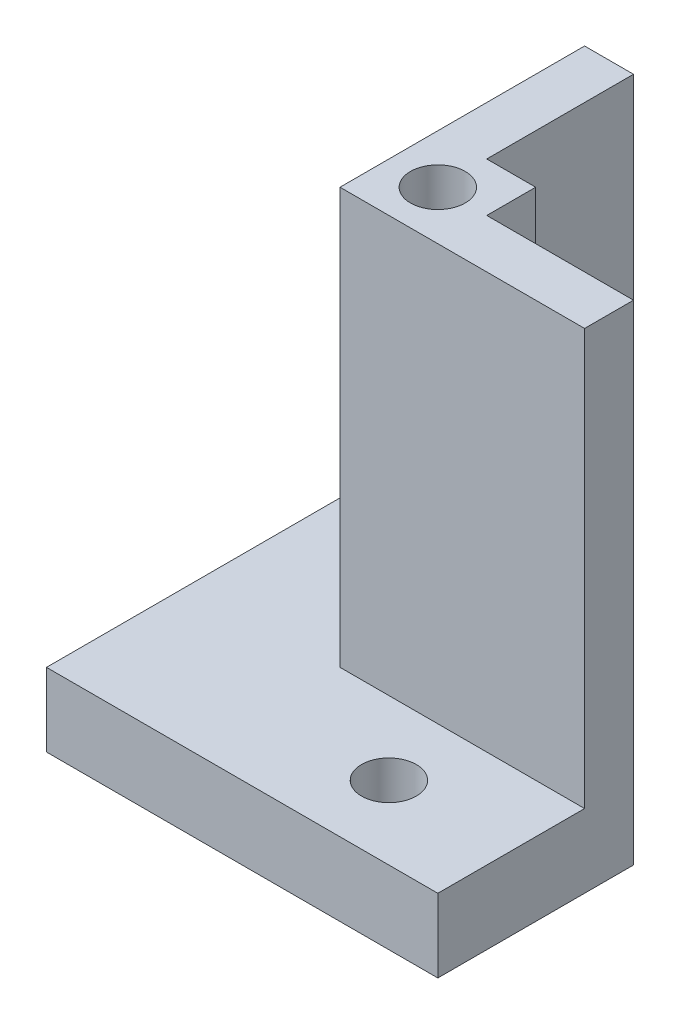
SolidWorks part; units mm, degrees
material "6061-T6 (SS)"
ref_plane "Front Plane" through (0, 0, 0) normal (0, 0, 1) x (1, 0, 0)
ref_plane "Top Plane" through (0, 0, 0) normal (0, 1, 0) x (1, 0, 0)
ref_plane "Right Plane" through (0, 0, 0) normal (1, 0, 0) x (0, 0, -1)
sketch "Sketch4" plane through (0, 0, 0) normal (0, 1, 0) x (1, 0, 0)
  line L0 (-2.7325, 2.4892) -> (-2.7325, 10.1092)
  line L5 (-2.7325, 10.1092) -> (-0.1925, 10.1092)
  line L6 (-0.1925, 10.1092) -> (-0.1925, 2.4892)
  line L8 (-2.7325, -2.5908) -> (-2.7325, 2.4892)
  line L9 (-0.1925, 2.4892) -> (2.3475, 2.4892)
  line L11 (-2.7325, -2.5908) -> (2.3475, 2.4892) construction
  line L12 (2.3475, -0.0508) -> (2.3475, 2.4892)
  line L13 (-2.7325, -2.5908) -> (2.3475, -2.5908)
  line L14 (9.9675, -0.0508) -> (2.3475, -0.0508)
  line L15 (9.9675, -2.5908) -> (9.9675, -0.0508)
  line L16 (2.3475, -2.5908) -> (9.9675, -2.5908)
  point P0 (0, 0)
  point P14 (-0.1417, 0.1417)
  dimension "D2" = 5.08
  dimension "D3" = 7.62
  dimension "D4" = 2.54
  dimension "D5" = 5.08
extrude "Boss-Extrude4" add sketch "Sketch4" along normal blind 25.4
sketch "Sketch5" plane through (0, 25.4, 0) normal (0, 1, 0) x (1, 0, 0)
  line L0 (2.3475, 2.4892) -> (-2.7325, -2.5908) construction
  circle A0 centre (-0.1925, -0.0508) radius 1.4224
  dimension "D1" = 2.8448
extrude "Cage Mounting Hole (4-40 Tapped)" cut sketch "Sketch5" against normal blind 3.81
sketch "Sketch6" plane through (0, 0, 0) normal (0, -1, 0) x (1, 0, 0)
  line L0 (9.9675, 2.5908) -> (9.9675, 10.2108)
  line L1 (9.9675, 10.2108) -> (-10.3525, 10.2108)
  line L2 (-10.3525, 10.2108) -> (-10.3525, -10.1092)
  line L3 (-10.3525, -10.1092) -> (-2.7325, -10.1092)
  line L4 (-0.1925, -10.1092) -> (-2.7325, -10.1092) construction
  line L5 (-2.7325, 2.5908) -> (-2.7325, -10.1092)
  line L6 (9.9675, 2.5908) -> (-2.7325, 2.5908)
  dimension "D1" = 7.62
  dimension "D2" = 7.62
extrude "Boss-Extrude5" add sketch "Sketch6" against normal blind 3.81
sketch "Sketch7" plane through (0, 3.81, 0) normal (0, 1, 0) x (1, 0, 0)
  line L0 (-2.7325, -2.5908) -> (-10.3525, 10.1092) construction
  line L1 (-2.7325, -2.5908) -> (9.9675, -10.2108) construction
  circle A0 centre (-6.5425, 3.7592) radius 1.4224
  circle A1 centre (3.6175, -6.4008) radius 1.4224
  circle A2 centre (-6.5425, 3.7592) radius 2.7813 construction
  dimension "D1" = 2.8448
  dimension "D2" = 2.8448
extrude "Base Mounting Holes (4-40 Clearance)" cut sketch "Sketch7" against normal blind 3.81 contours A0 | A1
equation "\"Height Needed for GPS\"=1"
equation "\"D1@Boss-Extrude4\"=\"Height Needed for GPS\""
